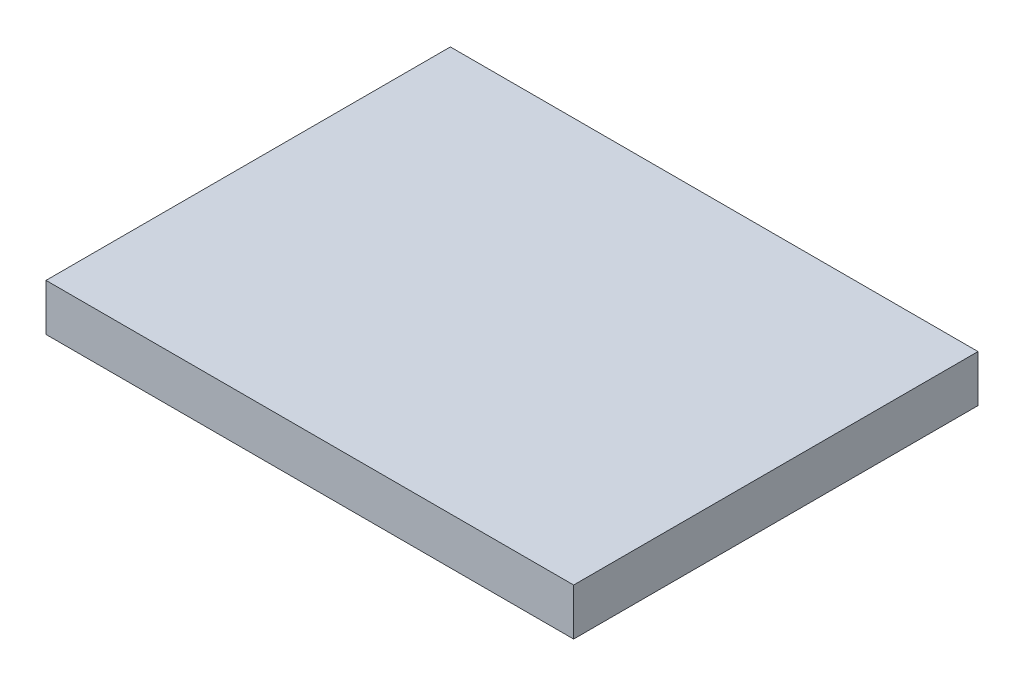
SolidWorks part; units mm, degrees
ref_plane "正面(Front)" through (0, 0, 0) normal (0, 0, 1) x (1, 0, 0)
ref_plane "平面(Top)" through (0, 0, 0) normal (0, 1, 0) x (1, 0, 0)
ref_plane "右側面(Right)" through (0, 0, 0) normal (1, 0, 0) x (0, 0, -1)
sketch "ｽｹｯﾁ1" plane through (0, 0, 0) normal (0, 1, 0) x (1, 0, 0)
  line L1 (53.5, 41) -> (-53.5, 41)
  line L2 (53.5, 41) -> (53.5, -41)
  line L3 (53.5, -41) -> (-53.5, -41)
  line L4 (-53.5, 41) -> (-53.5, -41)
  line L5 (53.5, 41) -> (-53.5, -41) construction
  line L6 (53.5, -41) -> (-53.5, 41) construction
  point P0 (0, 0)
  dimension "D1" = 82
  dimension "D2" = 107
extrude "ﾎﾞｽ - 押し出し1" add sketch "ｽｹｯﾁ1" along normal blind 9.5
